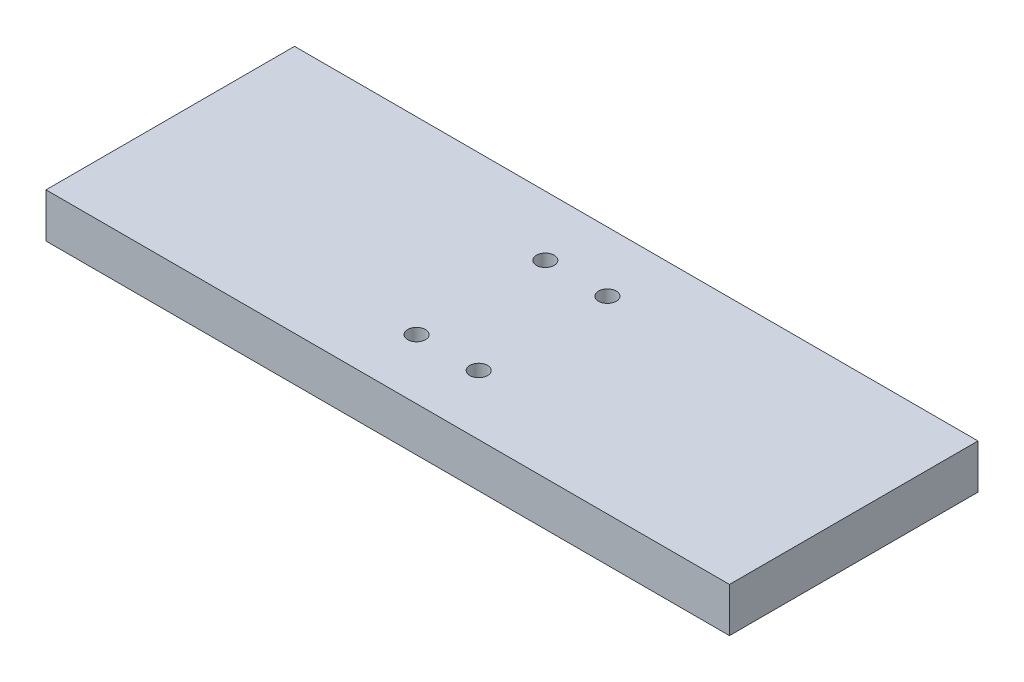
SolidWorks part; units mm, degrees
ref_plane "Front Plane" through (0, 0, 0) normal (0, 0, 1) x (1, 0, 0)
ref_plane "Top Plane" through (0, 0, 0) normal (0, 1, 0) x (1, 0, 0)
ref_plane "Right Plane" through (0, 0, 0) normal (1, 0, 0) x (0, 0, -1)
sketch "Sketch1" plane through (0, 0, 0) normal (0, 1, 0) x (1, 0, 0)
  line L1 (77, 28) -> (-77, 28)
  line L2 (77, 28) -> (77, -28)
  line L3 (77, -28) -> (-77, -28)
  line L4 (-77, 28) -> (-77, -28)
  line L5 (77, 28) -> (-77, -28) construction
  line L6 (77, -28) -> (-77, 28) construction
  point P0 (0, 0)
  dimension "D1" = 154
  dimension "D2" = 56
extrude "Boss-Extrude1" add sketch "Sketch1" along normal blind 10
sketch "Sketch4" plane through (0, 10, 0) normal (0, 1, 0) x (1, 0, 0)
  line L0 (77, 0) -> (-77, 0) construction
  line L1 (0, 28) -> (0, -28) construction
  line L2 (-77, 28) -> (-77, -28) construction
  line L3 (-77, -28) -> (77, -28) construction
  circle A0 centre (-27, 15) radius 2
  circle A1 centre (27, 15) radius 2
  circle A2 centre (27, -15) radius 2
  circle A3 centre (-27, -15) radius 2
  point P6 (0, 0)
  point P10 (0, 0)
  dimension "D1" = 4
  dimension "D2" = 27
  dimension "D3" = 15
hole_wizard "Ø4.0mm Dowel Hole3" positions "3DSketch3" profile "Sketch6" hole size "Ø4.0" standard "ANSI Metric"
sketch3d "3DSketch3"
  line L0 (0, 10, 28) -> (0, 10, -28) construction
  line L1 (-77, 10, 28) -> (77, 10, 28) construction
  line L2 (77, 10, -28) -> (-77, 10, -28) construction
  line L6 (-7, 10, -14.5) -> (-7, 10, 14.5) construction
  line L8 (-7, 10, 0) -> (0, 10, 0) construction
  point P0 (-7, 10, -14.5)
  point P2 (-7, 10, 14.5)
  point P4 (7, 10, 14.5)
  point P6 (7, 10, -14.5)
  dimension "D1" = 14
  dimension "D2" = 14
  dimension "D3" = 29
  dimension "D4" = 29
  dimension "D5" = 7
sketch "Sketch6" plane through (-7, 10, -14.5) normal (1, 0, 0) x (0, 0, 1)
  line L0 (0, 0) -> (0, 8.2017)
  line L1 (0, 8.2017) -> (2, 7)
  line L2 (2, 7) -> (2, 0)
  line L5 (2, 0) -> (0, 0)
  line L10 (0, 8.2017) -> (-2, 7) construction
  line L11 (0, -6.35) -> (0, 107.95) construction
  dimension "Hole Dia." = 4
  dimension "Hole Depth" = 7
  dimension "Drill Angle" = 118
cosmetic thread "Cosmetic Thread1" parameters "D1"=5, "D2"=5
cosmetic thread "Cosmetic Thread2" parameters "D1"=5, "D2"=5
cosmetic thread "Cosmetic Thread3" parameters "D1"=5, "D2"=5
cosmetic thread "Cosmetic Thread4" parameters "D1"=5, "D2"=5
